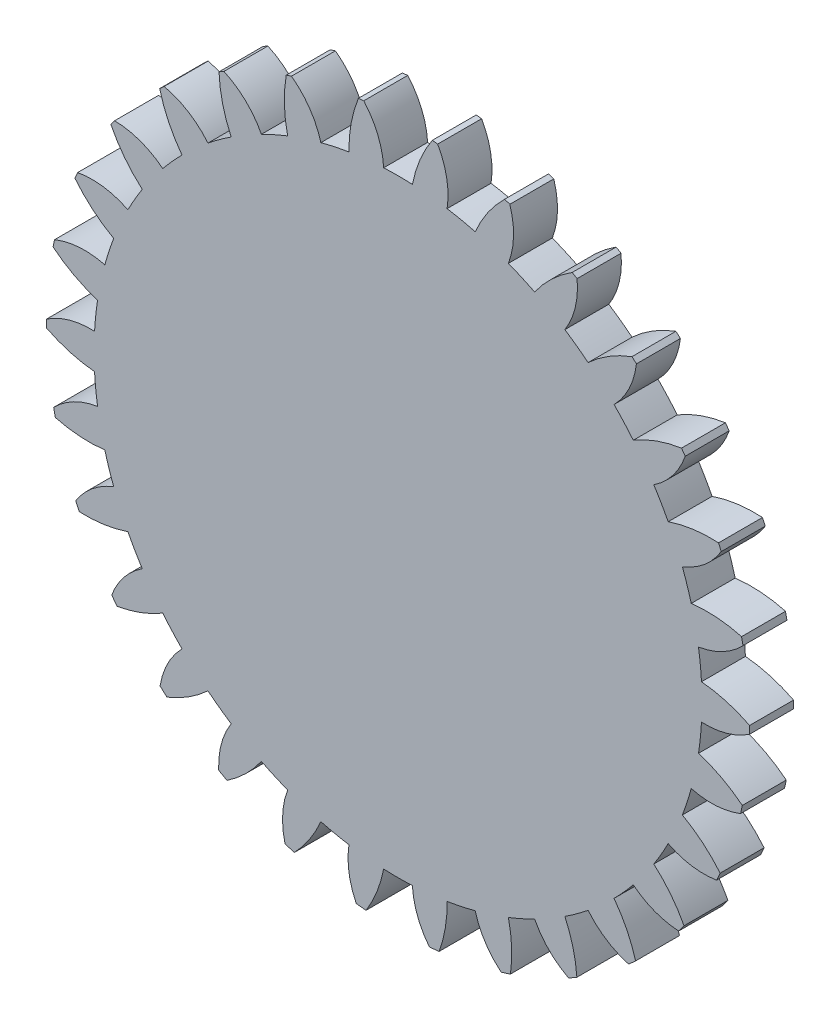
SolidWorks part; units mm, degrees
ref_plane "Front Plane" through (0, 0, 0) normal (0, 0, 1) x (1, 0, 0)
ref_plane "Top Plane" through (0, 0, 0) normal (0, 1, 0) x (1, 0, 0)
ref_plane "Right Plane" through (0, 0, 0) normal (1, 0, 0) x (0, 0, -1)
sketch "Sketch2" plane through (0, 0, 0) normal (0, 0, 1) x (1, 0, 0)
  circle A0 centre (0, 0) radius 609.6
  dimension "addendumDiameter" = 1219.2
extrude "Boss-Extrude2" add sketch "Sketch2" along normal blind 76.2
sketch "Sketch3" plane through (0, 0, 76.2) normal (0, 0, 1) x (1, 0, 0)
  line L0 (0, 0) -> (0, 1446.2572) construction
  line L1 (0, 0) -> (-144.6651, 1376.3962) construction
  line L2 (-26.2884, 536.3905) -> (-56.0482, 533.2626) construction
  circle A0 centre (0, 0) radius 540.3424 construction
  circle A1 centre (0, 0) radius 537.0343 construction
  circle A2 centre (0, 0) radius 523.875 construction
  arc A13 (24.9126, 523.2823) -> (-24.9126, 523.2823) centre (0, 0) ccw
  arc A14 (-59.3801, 606.7011) -> (59.3801, 606.7011) centre (0, 0) cw
  circle A15 centre (0, 0) radius 609.6 construction
  arc A16 (-59.3801, 606.7011) -> (-24.9126, 523.2823) centre (-161.8362, 515.5375) cw
  arc A17 (59.3801, 606.7011) -> (24.9126, 523.2823) centre (249.2639, 479.4136) ccw
  point P15 (-26.2884, 536.3905)
  dimension "D4" = 1047.75
  dimension "D5" = 1074.0687
  dimension "D2" = 228.6
  dimension "D3" = 29.9237
  dimension "D1" = 6
extrude "Cut-Extrude1" cut sketch "Sketch3" against normal through all contours A17 A13 A16 A14
sketch "Sketch4" plane through (0, 0, 0) normal (0, 0, -1) x (-1, 0, 0)
  point P0 (0, 0)
pattern_circular "CirPattern1" count 30 over 360 about axis through (-0.0062, -3.2102, 0) along (0, 0, 1) of "Cut-Extrude1"
equation "\"module\"= 1.5"
equation "\"teeth\"= 30"
equation "\"pressureAngle\"= 20deg"
equation "\"gearThickness\"= 3"
equation "\"addendumFactor\"= 1"
equation "\"dedendumFactor\"= 1.25"
equation "\"pitch\"= 1 / 1.5"
equation "\"pitchDiameter\"= \"teeth\"/\"pitch\""
equation "\"addendum\"= \"addendumFactor\" / \"pitch\""
equation "\"dendendum\"= \"dedendumFactor\" / \"pitch\""
equation "\"D1@Boss-Extrude2\"=\"gearThickness\""
equation "\"D3@Sketch3\"=PI / 2 / \"pitch\" / 2"
equation "\"D4@Sketch3\"=\"pitchDiameter\" - 2 * \"dendendum\""
equation "\"D5@Sketch3\"=\"pitchDiameter\" * cos ( \"pressureAngle\" )"
equation "\"D1@Sketch3\"=180/\"teeth\""
equation "\"D2@Sketch3\"=\"pitchDiameter\" / 5"
